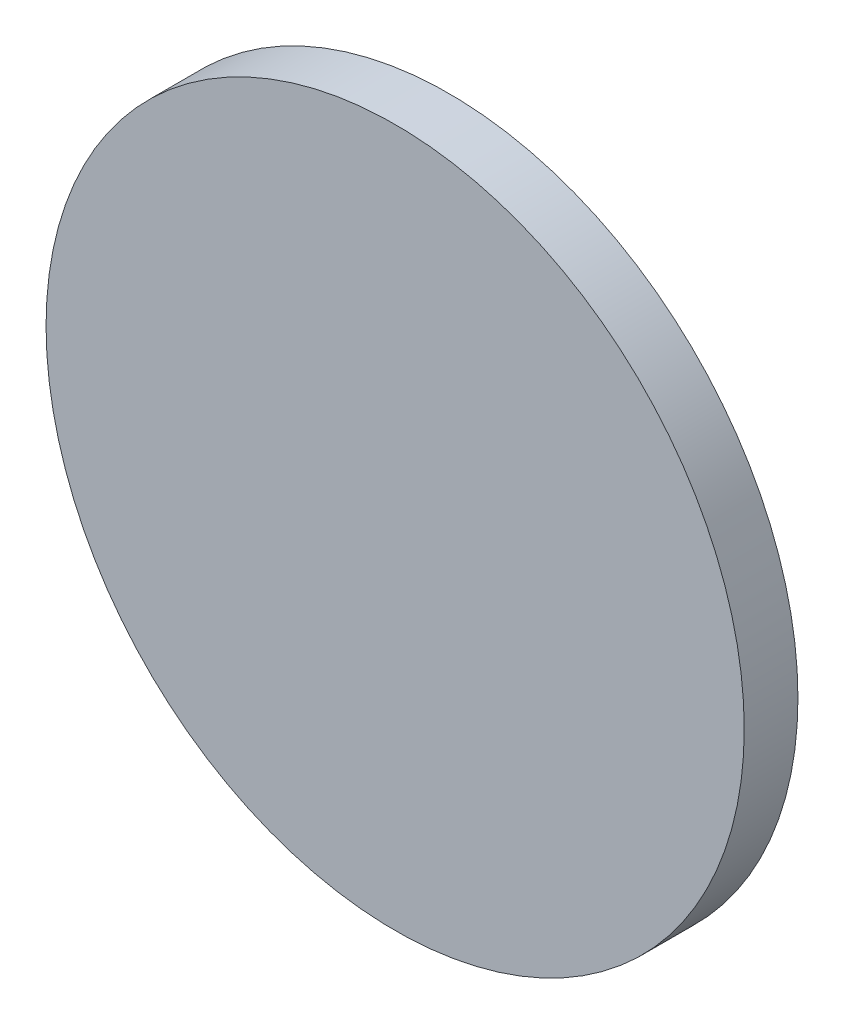
SolidWorks part; units mm, degrees
ref_plane "Front Plane" through (0, 0, 0) normal (0, 0, 1) x (1, 0, 0)
ref_plane "Top Plane" through (0, 0, 0) normal (0, 1, 0) x (1, 0, 0)
ref_plane "Right Plane" through (0, 0, 0) normal (1, 0, 0) x (0, 0, -1)
sketch "Sketch1" plane through (0, 0, 0) normal (0, 0, 1) x (1, 0, 0)
  circle A0 centre (0, 0) radius 13
  dimension "D1" = 26
extrude "Boss-Extrude1" add sketch "Sketch1" along normal blind 2
equation "\"inlet_diameter\"= 50"
equation "\"total_length\"=200"
equation "\"outlet_length\"=70"
equation "\"D2@Edge\"=\"outlet_length\""
equation "\"D1@Inlet\" = \"inlet_diameter\""
equation "\"outlet_diameter\"= 30"
equation "\"D1@Outlet\" = \"outlet_diameter\""
equation "\"side_length\"=120"
equation "\"D1@Sketch4\"=\"side_length\""
equation "\"D1@Sketch5\"=\"side_length\""
equation "\"inlet_lentgh\"=70"
equation "\"D1@Edge\"=\"inlet_lentgh\""
equation "\"D3@Edge\"=\"total_length\""
equation "\"D1@Sketch1\"=\"outlet_diameter\"-4"
